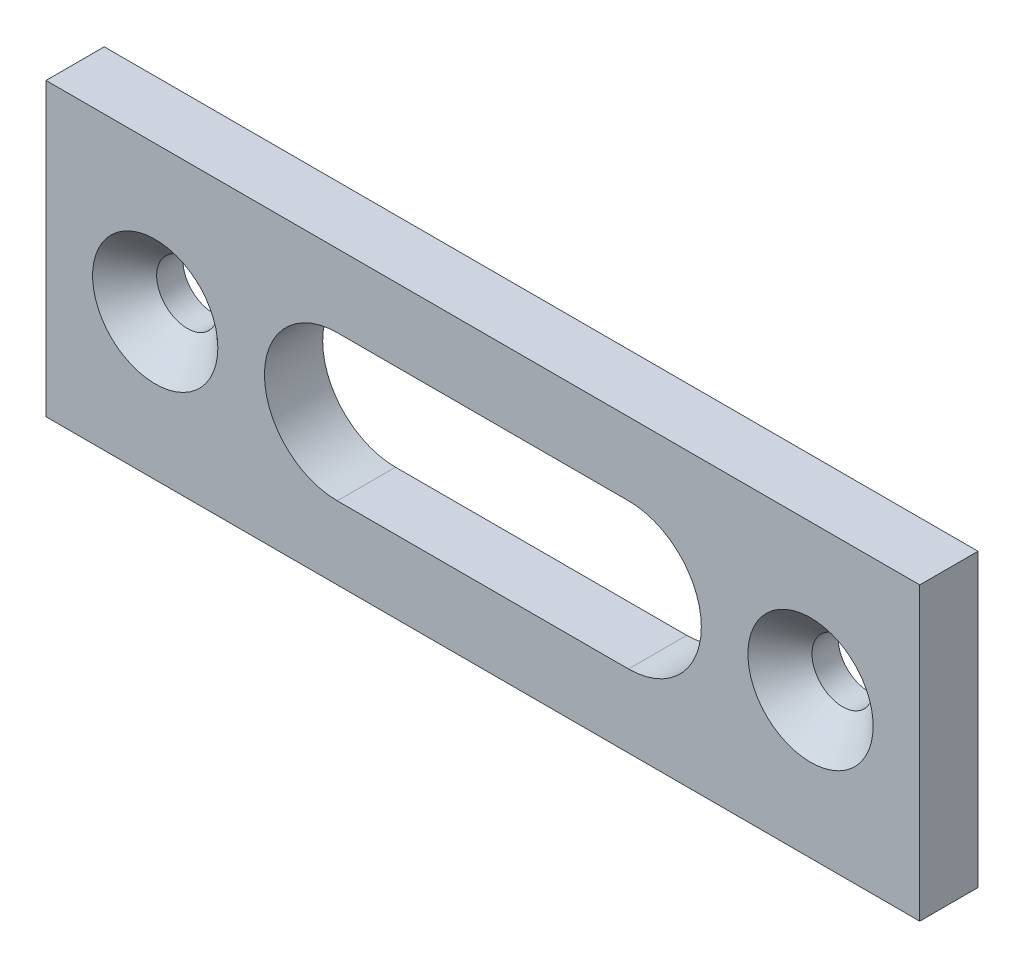
SolidWorks part; units mm, degrees
ref_plane "Plan de face" through (0, 0, 0) normal (0, 0, 1) x (1, 0, 0)
ref_plane "Plan de dessus" through (0, 0, 0) normal (0, 1, 0) x (1, 0, 0)
ref_plane "Plan de droite" through (0, 0, 0) normal (1, 0, 0) x (0, 0, -1)
sketch "Esquisse1" plane through (0, 0, 0) normal (0, 0, 1) x (1, 0, 0)
  line L0 (0, 10) -> (0, 0) construction
  line L1 (-30, 10) -> (30, 10)
  line L2 (-30, 10) -> (-30, -10)
  line L3 (-30, -10) -> (30, -10)
  line L4 (30, 10) -> (30, -10)
  line L5 (0, 0) -> (-30, 0) construction
  line L6 (0, 0) -> (22.5, 0) construction
  line L7 (-10, 5) -> (10, 5)
  line L8 (-10, -5) -> (10, -5)
  circle A0 centre (-22.5, 0) radius 2.1
  circle A1 centre (22.5, 0) radius 2.1
  arc A2 (-10, 5) -> (-10, -5) centre (-10, 0) ccw
  arc A3 (10, -5) -> (10, 5) centre (10, 0) ccw
  dimension "D3" = 4.2
  dimension "D4" = 45
  dimension "D6" = 10
  dimension "D7" = 20
  dimension "D8" = 20
  dimension "D1" = 60
  dimension "D2" = 20
  dimension "D5" = 22.5
extrude "Extrusion1" add sketch "Esquisse1" along normal blind 4
chamfer "Chanfrein1" distance 2.2 angle 45 2 edges at (-20.4, 0, 4) (24.6, 0, 4)
